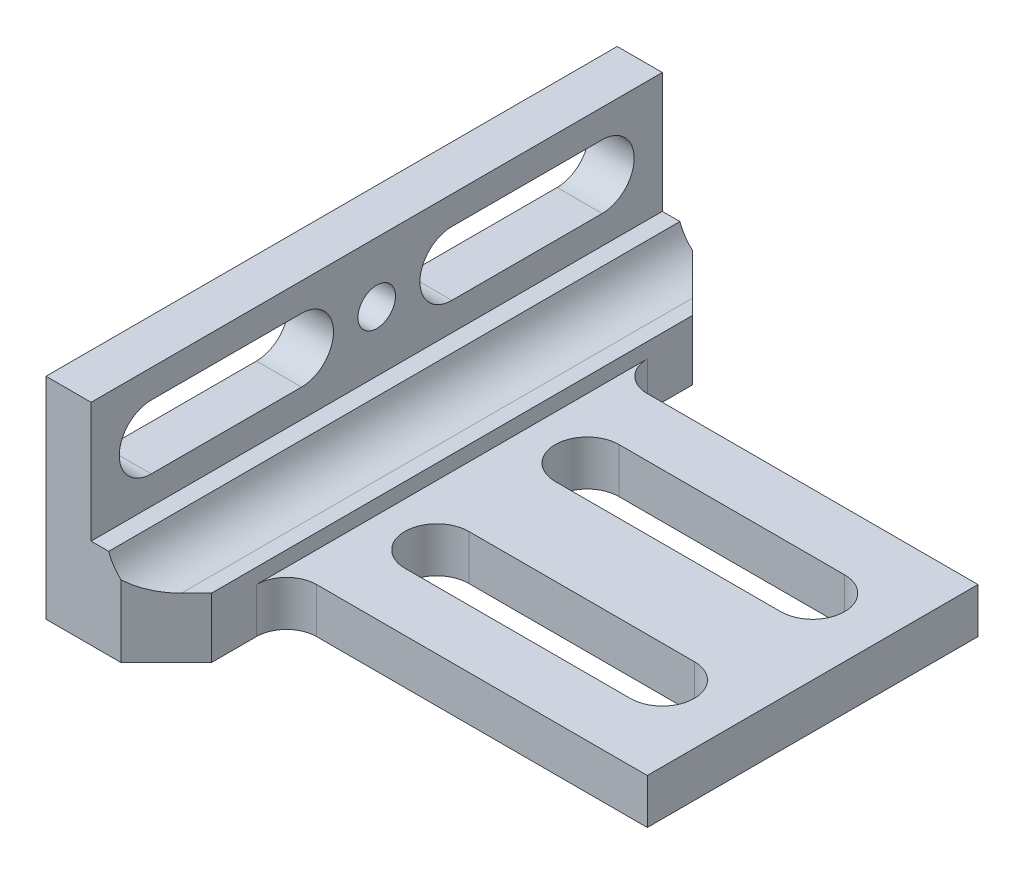
SolidWorks part; units mm, degrees
material "AISI 1018 Steel, Cold Rolled"
ref_plane "Plane1" through (0, 0, 0) normal (0, 0, 1) x (1, 0, 0)
ref_plane "Plane2" through (0, 0, 0) normal (0, 1, 0) x (1, 0, 0)
ref_plane "Plane3" through (0, 0, 0) normal (1, 0, 0) x (0, 0, -1)
sketch "Sketch1" plane through (0, 0, 0) normal (0, 0, 1) x (1, 0, 0)
  line L0 (0, 0) -> (0, 101.6)
  line L1 (0, 101.6) -> (3.1801, 101.6)
  line L2 (12.7, 92.0801) -> (12.7, 22.225)
  line L3 (22.225, 12.7) -> (101.6, 12.7)
  line L4 (101.6, 12.7) -> (101.6, 0)
  line L5 (101.6, 0) -> (0, 0)
  arc A1 (3.1801, 101.6) -> (12.7, 92.0801) centre (3.1801, 92.0801) cw
  arc A2 (22.225, 12.7) -> (12.7, 22.225) centre (22.225, 22.225) cw
  circle A3 centre (0, 0) radius 9.525 construction
  dimension "Radius_1" = 9.525
  dimension "Radius_2" = 9.525
  dimension "D1" = 12.7
  dimension "V_leg" = 101.6
  dimension "H_leg" = 101.6
  dimension "Thickness" = 12.7
  dimension "Flat_wid" = 3.1801
extrude "BaseSteelAngle" add sketch "Sketch1" along normal mid plane 120.65
sketch "Sketch2" plane through (0, 0, 60.325) normal (0, 0, 1) x (1, 0, 0)
  line L0 (-4.1123, 44.45) -> (18.4083, 44.45)
  line L1 (0, 0) -> (101.6, 0) construction
  dimension "D1" = 44.45
extrude "Cut-Extrude1" cut sketch "Sketch2" against normal through all and the other way through all
sketch "Sketch4" plane through (78.1669, 12.7, 45.2817) normal (0, 1, 0) x (0, 0, 1)
  line L0 (-67.903, 7.5581) -> (-67.903, -40.0669)
  line L1 (-54.4105, -40.0669) -> (-54.4105, 7.5581)
  line L2 (-45.2817, -128.1669) -> (-45.2817, -28.1669) construction
  line L4 (-105.6067, -78.1669) -> (15.0433, -78.1669) construction
  arc A0 (-54.4105, 7.5581) -> (-67.903, 7.5581) centre (-61.1567, 7.5581) ccw
  arc A1 (-67.903, -40.0669) -> (-54.4105, -40.0669) centre (-61.1567, -40.0669) ccw
  dimension "D3" = 6.7462
  dimension "D2" = 38.1
  dimension "D4" = 47.625
  dimension "D1" = 15.875
extrude "Cut-Extrude3" cut sketch "Sketch4" against normal through all
mirror "Mirror1" about plane through (0, 0, 0) normal (0, 0, 1) of "Cut-Extrude3"
sketch "Sketch5" plane through (0, 0, -60.325) normal (0, 0, -1) x (-1, 0, 0)
  line L0 (0, 0) -> (-101.6, 0) construction
  line L1 (-101.6, 15.875) -> (-25.4, 15.875)
  line L2 (-101.6, 15.875) -> (-101.6, 9.525)
  line L3 (-101.6, 9.525) -> (-25.4, 9.525)
  line L4 (-25.4, 15.875) -> (-25.4, 9.525)
  line L6 (0, 44.45) -> (0, 0) construction
  line L7 (-101.6, 0) -> (-101.6, 12.7) construction
  dimension "D1" = 9.525
  dimension "D2" = 25.4
  dimension "D3" = 6.35
extrude "Cut-Extrude4" cut sketch "Sketch5" against normal through all
sketch "Sketch6" plane through (0, 0, -60.325) normal (0, 0, -1) x (-1, 0, 0)
  line L0 (-12.7, 22.225) -> (-12.7, 44.45) construction
  line L1 (-19.05, 47.625) -> (-9.525, 47.625)
  line L2 (-19.05, 47.625) -> (-19.05, 19.05)
  line L3 (-19.05, 19.05) -> (-9.525, 19.05)
  line L4 (-9.525, 47.625) -> (-9.525, 19.05)
  line L5 (0, 44.45) -> (-12.7, 44.45) construction
  dimension "D1" = 3.175
  dimension "D2" = 25.4
  dimension "D3" = 6.35
  dimension "D4" = 3.175
extrude "Cut-Extrude5" cut sketch "Sketch6" against normal through all
sketch "Sketch7" plane through (9.525, 0, 0) normal (1, 0, 0) x (0, 0, -1)
  line L0 (15.875, 25.0031) -> (47.625, 25.0031)
  line L1 (15.875, 38.4969) -> (47.625, 38.4969)
  line L5 (0, 0) -> (0, 31.75) construction
  line L6 (15.875, 31.75) -> (0, 31.75) construction
  line L7 (60.325, 44.45) -> (-60.325, 44.45) construction
  arc A0 (15.875, 38.4969) -> (15.875, 25.0031) centre (15.875, 31.75) ccw
  arc A1 (47.625, 25.0031) -> (47.625, 38.4969) centre (47.625, 31.75) ccw
  dimension "D4" = 6.7469
  dimension "D1" = 12.7
  dimension "D2" = 15.875
  dimension "D3" = 31.75
extrude "Cut-Extrude6" cut sketch "Sketch7" against normal through all
mirror "Mirror2" about plane through (0, 0, 0) normal (0, 0, 1) of "Cut-Extrude6"
hole_wizard "3/8-16 Tapped Hole1" positions "Sketch9" profile "Sketch8" tap size "3/8-16" standard "Ansi Inch" end condition through all
sketch "Sketch9" plane through (9.525, 0, 0) normal (1, 0, 0) x (0, 0, -1)
  line L0 (0, 50) -> (0, -50) construction
  line L5 (0, 31.75) -> (-15.875, 31.75) construction
  line L6 (0, 31.75) -> (0, 0) construction
  point P0 (0, 31.75)
cosmetic thread "Cosmetic Thread1" parameters "D2"=9.525
sketch "Sketch8" plane through (9.525, 31.75, 0) normal (0, 1, 0) x (0, 0, -1)
  line L0 (0, 0) -> (0, 9.525)
  line L1 (0, 9.525) -> (3.9687, 9.525)
  line L2 (3.9687, 9.525) -> (3.9687, 0)
  line L5 (3.9687, 0) -> (0, 0)
  line L11 (0, -6.35) -> (0, 107.95) construction
  dimension "Thru Tap Drill Dia." = 7.9375
  dimension "Thru Tap Drill Depth" = 9.525
sketch "Sketch11" plane through (101.6, 0, 0) normal (1, 0, 0) x (0, 0, -1)
  line L0 (-60.325, 0) -> (60.325, 0) construction
  line L1 (60.325, 0) -> (34.925, 0)
  line L2 (60.325, 0) -> (60.325, 9.525)
  line L3 (60.325, 9.525) -> (34.925, 9.525)
  line L4 (34.925, 0) -> (34.925, 9.525)
  line L5 (-60.325, 0) -> (-34.925, 0)
  line L6 (-60.325, 0) -> (-60.325, 9.525)
  line L7 (-60.325, 9.525) -> (-34.925, 9.525)
  line L8 (-34.925, 0) -> (-34.925, 9.525)
  line L9 (-60.325, 9.525) -> (60.325, 9.525) construction
  line L10 (60.325, 0) -> (60.325, 9.525) construction
  line L11 (-60.325, 0) -> (-60.325, 9.525) construction
  dimension "D1" = 25.4
  dimension "D2" = 25.4
extrude "Cut-Extrude8" cut sketch "Sketch11" against normal up to surface (76.2 mm away) up to face at (25.4, 11.1125, 0)
fillet "Fillet2" radius 6.35 2 edges at (25.4, 4.7625, -34.925) (25.4, 4.7625, 34.925)
chamfer "Chamfer3" distance 9.525 angle 45 2 edges at (25.4, 6.35, 60.325) (25.4, 6.35, -60.325)
